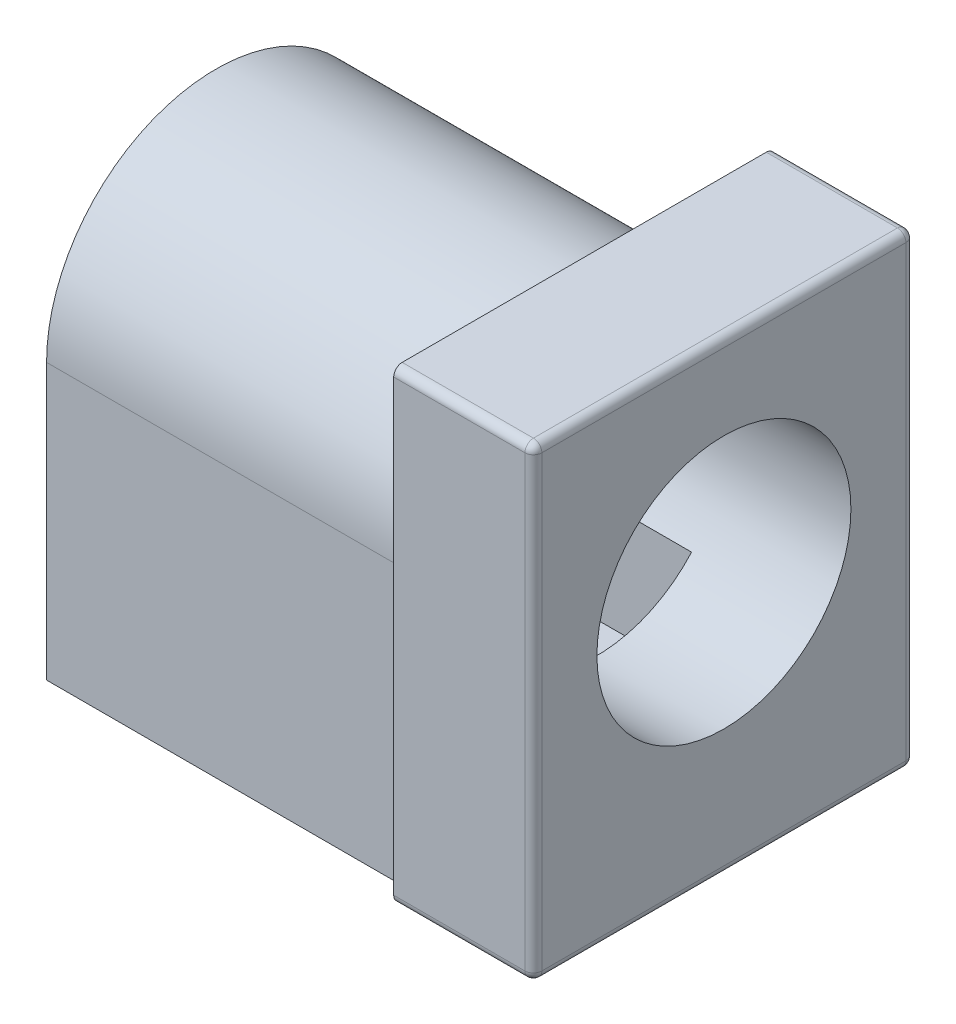
SolidWorks part; units mm, degrees
ref_plane "Front" through (0, 0, 0) normal (0, 0, 1) x (1, 0, 0)
ref_plane "Top" through (0, 0, 0) normal (0, 1, 0) x (1, 0, 0)
ref_plane "Right" through (0, 0, 0) normal (1, 0, 0) x (0, 0, -1)
sketch "Sketch1" plane through (0, 0, 0) normal (1, 0, 0) x (0, 0, -1)
  line L1 (0, 0) -> (9, 0)
  line L2 (0, 0) -> (0, 11)
  line L3 (0, 11) -> (9, 11)
  line L4 (9, 0) -> (9, 11)
  dimension "D1" = 9
  dimension "D2" = 11
extrude "Boss-Extrude1" add sketch "Sketch1" along normal blind 12
sketch "Sketch2" plane through (0, 0, 0) normal (-1, 0, 0) x (0, 0, 1)
  line L3 (-8.5, 6.5) -> (-8.5, 0)
  line L4 (-0.5, 6.5) -> (-0.5, 0)
  line L5 (-8.5, 6.5) -> (-0.5, 6.5) construction
  line L6 (-8.5, 0) -> (-0.5, 0) construction
  line L7 (0, 0) -> (-9, 0) construction
  line L8 (-9, 0) -> (-9, 11) construction
  line L9 (-9, 11) -> (0, 11) construction
  arc A0 (-8.5, 6.5) -> (-0.5, 6.5) centre (-4.5, 6.5) cw
  dimension "D1" = 4.5
  dimension "D2" = 8
  dimension "D3" = 0.5
extrude "Cut-Extrude1" cut sketch "Sketch2" against normal blind 8.7 and the other way through all
sketch "Sketch3" plane through (12, 0, 0) normal (1, 0, 0) x (0, 0, -1)
  line L0 (4.5, 11) -> (4.5, 0) construction
  line L1 (9, 11) -> (0, 11) construction
  line L2 (0, 0) -> (9, 0) construction
  circle A0 centre (4.5, 6) radius 3
  dimension "D1" = 6
  dimension "D2" = 5
extrude "Cut-Extrude2" cut sketch "Sketch3" against normal through all
sketch "Sketch4" plane through (0, 0, 0) normal (0, -1, 0) x (-1, 0, 0)
  line L1 (-4.75, 3) -> (-5.25, 3)
  line L2 (-4.75, 3) -> (-4.75, 6)
  line L3 (-4.75, 6) -> (-5.25, 6)
  line L4 (-5.25, 3) -> (-5.25, 6)
  line L5 (-5, 3) -> (-5, 6) construction
  line L6 (-12, 0) -> (-12, 9) construction
  line L7 (0, 4.5) -> (-12, 4.5) construction
  line L8 (0, 0.5) -> (0, 8.5) construction
  line L9 (-4.75, 4.5) -> (-5.25, 4.5) construction
  point P4 (-12, 4.5)
  dimension "D1" = 7
  dimension "D2" = 0.5
  dimension "D3" = 3
extrude "Cut-Extrude3" cut sketch "Sketch4" against normal up to next
fillet "Fillet1" radius 0.2 8 edges at (10.35, 0, 0) (12, 5.5, 0) (12, 0, -4.5) (10.35, 0, -9) (12, 11, -4.5) (12, 5.5, -9) (10.35, 11, -9) (10.35, 11, 0)
sketch "Sketch5" plane through (0, 0, -8.5) normal (0, 0, -1) x (-1, 0, 0)
  line L0 (0, 0) -> (-8.7, 0) construction
  line L1 (-3, 4) -> (0, 4)
  line L2 (-3, 4) -> (-3, 3.5)
  line L3 (-3, 3.5) -> (0, 3.5)
  line L4 (0, 4) -> (0, 3.5)
  line L5 (-12, 0.2) -> (-12, 10.8) construction
  dimension "D1" = 3
  dimension "D2" = 0.5
  dimension "D3" = 4
  dimension "D4" = 9
extrude "Cut-Extrude4" cut sketch "Sketch5" against normal up to next
sketch "Sketch6" plane through (0, 0, 0) normal (-1, 0, 0) x (0, 0, 1)
  line L1 (-6.7361, 4) -> (-2.2639, 4)
  line L2 (-6.7361, 4) -> (-6.7361, 1.5)
  line L3 (-6.7361, 1.5) -> (-2.2639, 1.5)
  line L4 (-2.2639, 4) -> (-2.2639, 1.5)
  arc A0 (-6.1583, 3.5) -> (-6.7361, 4) centre (-4.5, 6) ccw construction
  dimension "D1" = 2.5
extrude "Cut-Extrude5" cut sketch "Sketch6" against normal blind 9
